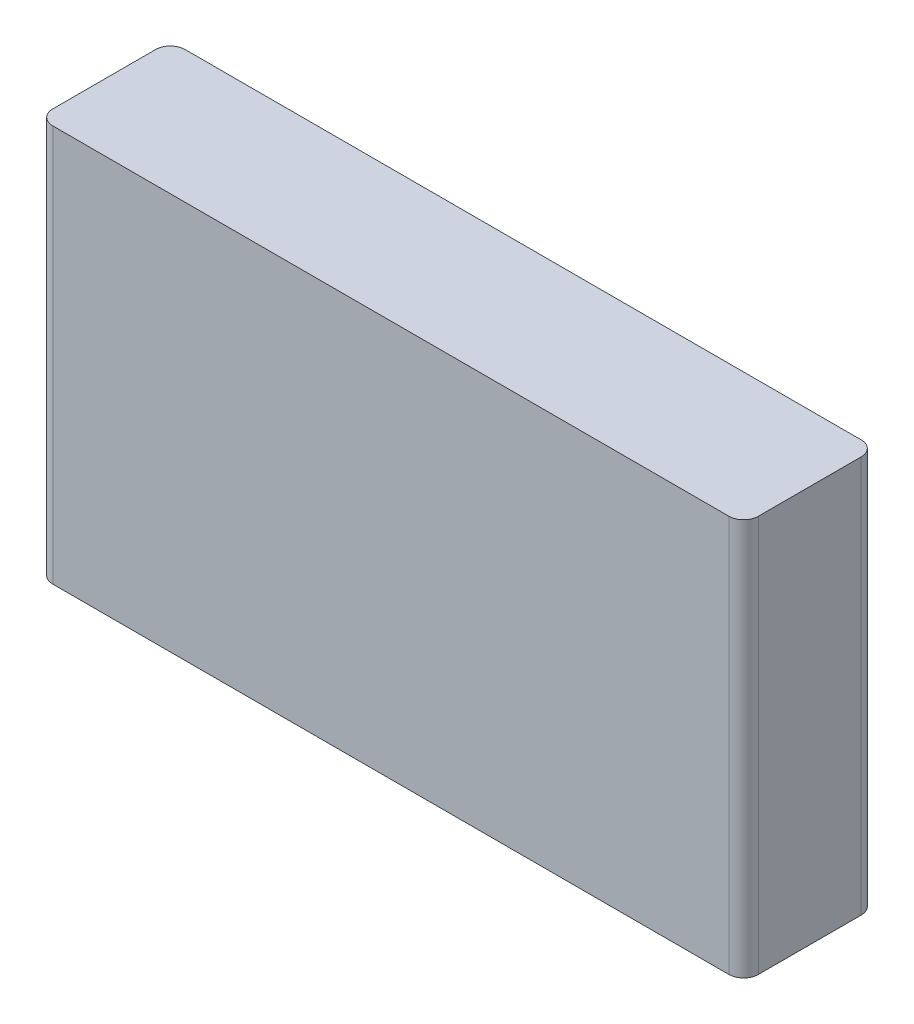
SolidWorks part; units mm, degrees
ref_plane "Front Plane" through (0, 0, 0) normal (0, 0, 1) x (1, 0, 0)
ref_plane "Top Plane" through (0, 0, 0) normal (0, 1, 0) x (1, 0, 0)
ref_plane "Right Plane" through (0, 0, 0) normal (1, 0, 0) x (0, 0, -1)
sketch "Sketch1" plane through (0, 0, 0) normal (0, 0, 1) x (1, 0, 0)
  line L1 (-24, 13.5) -> (24, 13.5)
  line L2 (-24, 13.5) -> (-24, -13.5)
  line L3 (-24, -13.5) -> (24, -13.5)
  line L4 (24, 13.5) -> (24, -13.5)
  line L5 (-24, 13.5) -> (24, -13.5) construction
  line L6 (-24, -13.5) -> (24, 13.5) construction
  point P0 (0, 0)
  dimension "D1" = 48
  dimension "D2" = 27
extrude "Boss-Extrude1" add sketch "Sketch1" along normal blind 9
fillet "Fillet1" radius 1 4 edges at (-24, 0, 0) (-24, 0, 9) (24, 0, 0) (24, 0, 9)
